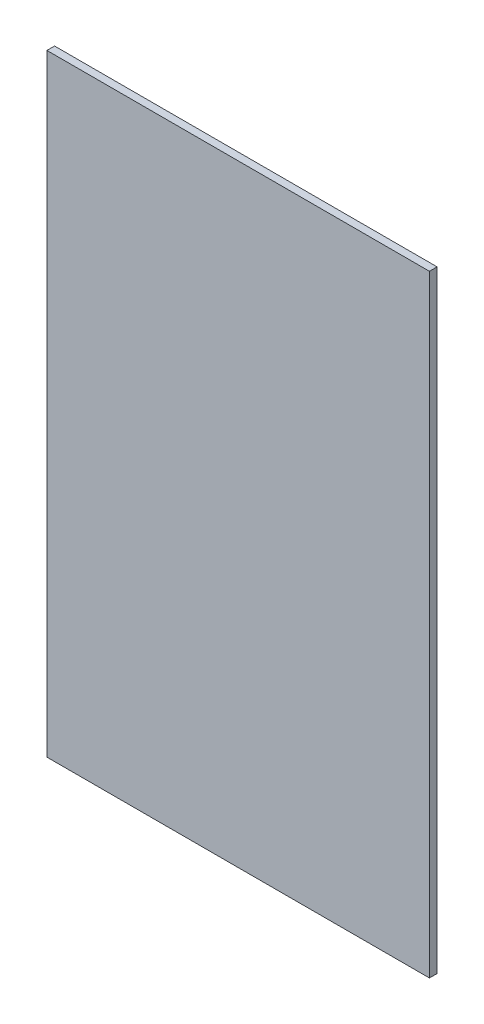
SolidWorks part; units mm, degrees
ref_plane "Front Plane" through (0, 0, 0) normal (0, 0, 1) x (1, 0, 0)
ref_plane "Top Plane" through (0, 0, 0) normal (0, 1, 0) x (1, 0, 0)
ref_plane "Right Plane" through (0, 0, 0) normal (1, 0, 0) x (0, 0, -1)
sketch "Croquis1" plane through (0, 0, 0) normal (0, 0, 1) x (1, 0, 0)
  line L0 (-125, -200) -> (-125, 200)
  line L1 (-125, -200) -> (125, -200)
  line L2 (-125, 200) -> (125, 200)
  line L3 (125, -200) -> (125, 200)
  line L4 (-125, -200) -> (125, 200) construction
  line L5 (-125, 200) -> (125, -200) construction
  point P1 (0, 0)
  dimension "D1" = 400
  dimension "D2" = 250
extrude "Saliente-Extruir1" add sketch "Croquis1" along normal blind 5
